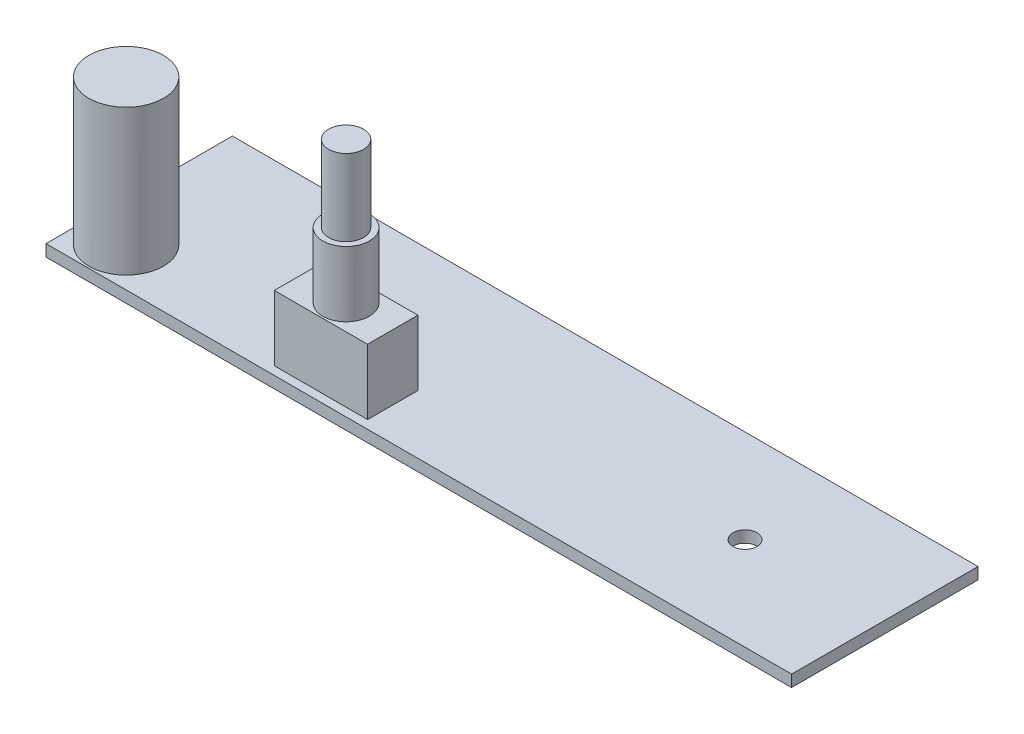
SolidWorks part; units mm, degrees
ref_plane "Front Plane" through (0, 0, 0) normal (0, 0, 1) x (1, 0, 0)
ref_plane "Top Plane" through (0, 0, 0) normal (0, 1, 0) x (1, 0, 0)
ref_plane "Right Plane" through (0, 0, 0) normal (1, 0, 0) x (0, 0, -1)
sketch "Sketch1" plane through (0, 0, 0) normal (0, 1, 0) x (1, 0, 0)
  line L1 (0, 0) -> (101.6, 0)
  line L2 (0, 0) -> (0, 25.4)
  line L3 (0, 25.4) -> (101.6, 25.4)
  line L4 (101.6, 0) -> (101.6, 25.4)
  dimension "D1" = 101.6
  dimension "D2" = 25.4
extrude "Boss-Extrude1" add sketch "Sketch1" along normal blind 1.5875
hole_wizard "#4 Clearance Hole2" positions "Sketch4" profile "Sketch3" hole size "#4" standard "ANSI Inch" end condition up to next
sketch "Sketch4" plane through (0, 1.5875, 0) normal (0, 1, 0) x (1, 0, 0)
  line L1 (31.75, 12.7) -> (82.55, 12.7)
  line L3 (101.6, 0) -> (101.6, 25.4) construction
  point P0 (31.75, 12.7)
  point P2 (82.55, 12.7)
  point P13 (101.6, 12.7)
  dimension "D1" = 19.05
  dimension "D2" = 69.85
sketch "Sketch3" plane through (31.75, 1.5875, -12.7) normal (1, 0, 0) x (0, 0, 1)
  line L0 (0, 0) -> (0, 1.5875)
  line L1 (0, 1.5875) -> (1.6319, 1.5875)
  line L2 (1.6319, 1.5875) -> (1.6319, 0)
  line L5 (1.6319, 0) -> (0, 0)
  line L11 (0, -6.35) -> (0, 107.95) construction
  dimension "Thru Hole Dia." = 3.2639
  dimension "Thru Hole Depth" = 1.5875
sketch "Sketch5" plane through (0, 1.5875, 0) normal (0, 1, 0) x (1, 0, 0)
  line L0 (101.6, 25.4) -> (0, 25.4) construction
  line L1 (101.6, 0) -> (101.6, 25.4) construction
  circle A0 centre (5.588, 5.334) radius 5.08
  dimension "D1" = 20.066
  dimension "D3" = 10.16
  dimension "D2" = 96.012
extrude "Boss-Extrude2" add sketch "Sketch5" along normal blind 19.812
sketch "Sketch6" plane through (0, 1.5875, 0) normal (0, 1, 0) x (1, 0, 0)
  line L0 (101.6, 0) -> (101.6, 25.4) construction
  line L1 (42.672, 8.001) -> (29.972, 8.001)
  line L2 (42.672, 8.001) -> (42.672, 1.143)
  line L3 (42.672, 1.143) -> (29.972, 1.143)
  line L4 (29.972, 8.001) -> (29.972, 1.143)
  line L5 (42.672, 8.001) -> (29.972, 1.143) construction
  line L6 (42.672, 1.143) -> (29.972, 8.001) construction
  line L7 (101.6, 25.4) -> (0, 25.4) construction
  point P0 (36.322, 4.572)
  dimension "D1" = 65.278
  dimension "D2" = 20.828
  dimension "D3" = 6.858
  dimension "D4" = 12.7
extrude "Boss-Extrude3" add sketch "Sketch6" along normal blind 8.89
sketch "Sketch7" plane through (0, 10.4775, 0) normal (0, 1, 0) x (1, 0, 0)
  line L0 (36.322, 1.143) -> (36.322, 8.001) construction
  line L4 (29.972, 8.001) -> (29.972, 1.143)
  line L5 (29.972, 1.143) -> (42.672, 1.143)
  line L6 (42.672, 1.143) -> (42.672, 8.001)
  line L7 (42.672, 8.001) -> (29.972, 8.001)
  line L8 (29.972, 8.001) -> (29.972, 1.143)
  line L9 (29.972, 1.143) -> (42.672, 1.143)
  line L10 (42.672, 1.143) -> (42.672, 8.001)
  line L11 (42.672, 8.001) -> (29.972, 8.001)
  circle A0 centre (36.322, 4.572) radius 3.175
  point P6 (0, 0)
  dimension "D2" = 6.35
  dimension "D1" = 0
extrude "Boss-Extrude4" add sketch "Sketch7" along normal blind 8.89 contours L0 A0 | A0 L0
sketch "Sketch8" plane through (0, 19.3675, 0) normal (0, 1, 0) x (1, 0, 0)
  circle A0 centre (36.322, 4.572) radius 2.3812
  dimension "D1" = 4.7625
extrude "Boss-Extrude5" add sketch "Sketch8" along normal blind 10.414
sketch "Sketch11" plane through (0, 1.5875, 0) normal (0, 1, 0) x (1, 0, 0)
  line L0 (101.6, 12.7) -> (0, 12.7) construction
  line L1 (57.912, 22.098) -> (91.44, 22.098)
  line L2 (57.912, 22.098) -> (57.912, 3.302)
  line L3 (57.912, 3.302) -> (91.44, 3.302)
  line L4 (91.44, 22.098) -> (91.44, 3.302)
  line L5 (57.912, 22.098) -> (91.44, 3.302) construction
  line L6 (57.912, 3.302) -> (91.44, 22.098) construction
  line L7 (101.6, 0) -> (101.6, 25.4) construction
  line L8 (0, 25.4) -> (0, 0) construction
  point P0 (74.676, 12.7)
  dimension "D1" = 18.796
  dimension "D2" = 33.528
  dimension "D3" = 10.16
sketch "Sketch12" plane through (0, 1.5875, 0) normal (0, 1, 0) x (1, 0, 0)
  line L0 (91.44, 22.098) -> (91.44, 3.302) construction
  line L1 (57.912, 22.098) -> (91.44, 22.098) construction
  line L2 (57.912, 22.098) -> (57.912, 3.302) construction
  line L3 (57.912, 3.302) -> (91.44, 3.302) construction
  line L4 (91.44, 22.098) -> (91.44, 3.302)
  line L5 (57.912, 22.098) -> (91.44, 22.098)
  line L6 (57.912, 22.098) -> (57.912, 3.302)
  line L7 (57.912, 3.302) -> (91.44, 3.302)
